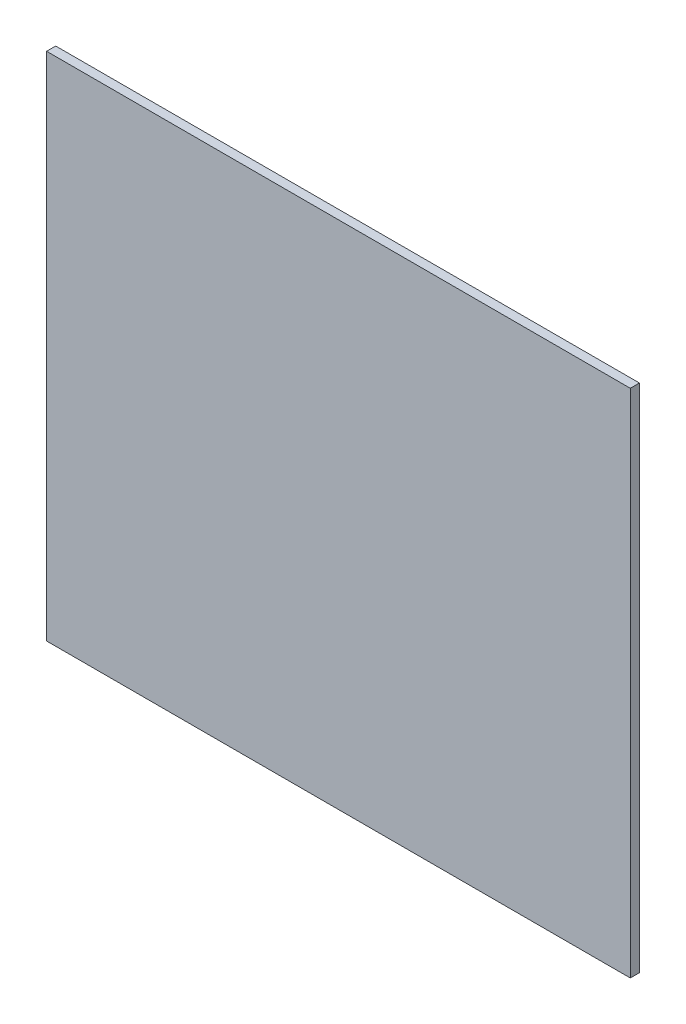
SolidWorks part; units mm, degrees
ref_plane "Front Plane" through (0, 0, 0) normal (0, 0, 1) x (1, 0, 0)
ref_plane "Top Plane" through (0, 0, 0) normal (0, 1, 0) x (1, 0, 0)
ref_plane "Right Plane" through (0, 0, 0) normal (1, 0, 0) x (0, 0, -1)
sketch "Sketch1" plane through (0, 0, 0) normal (0, 0, 1) x (1, 0, 0)
  line L1 (-35.6801, 24.7288) -> (167.5199, 24.7288)
  line L2 (-35.6801, 24.7288) -> (-35.6801, -153.0712)
  line L3 (-35.6801, -153.0712) -> (167.5199, -153.0712)
  line L4 (167.5199, 24.7288) -> (167.5199, -153.0712)
  dimension "D1" = 203.2
  dimension "D2" = 177.8
extrude "Boss-Extrude1" add sketch "Sketch1" along normal blind 3.175
